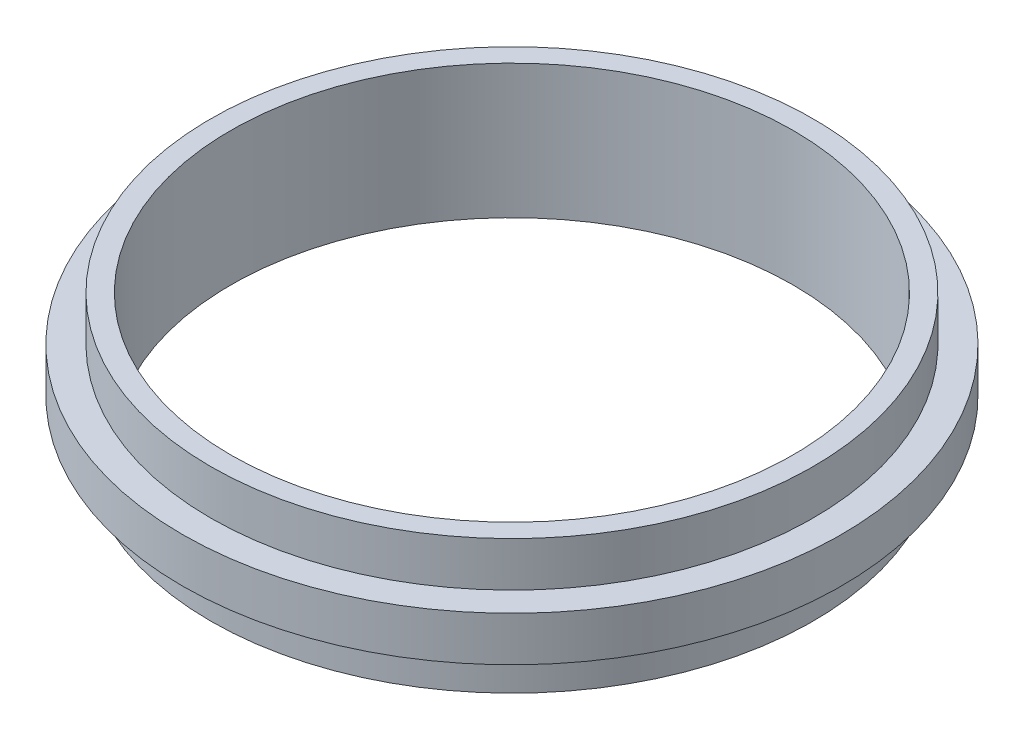
SolidWorks part; units mm, degrees
ref_plane "Front Plane" through (0, 0, 0) normal (0, 0, 1) x (1, 0, 0)
ref_plane "Top Plane" through (0, 0, 0) normal (0, 1, 0) x (1, 0, 0)
ref_plane "Right Plane" through (0, 0, 0) normal (1, 0, 0) x (0, 0, -1)
sketch "Sketch1" plane through (0, 0, 0) normal (0, 1, 0) x (1, 0, 0)
  circle A0 centre (0, 0) radius 93.7895
  circle A1 centre (0, 0) radius 80.01
  dimension "D1" = 187.579
  dimension "D2" = 160.02
extrude "Boss-Extrude1" add sketch "Sketch1" along normal mid plane 12.7
sketch "Sketch2" plane through (0, 6.35, 0) normal (0, 1, 0) x (1, 0, 0)
  circle A0 centre (0, 0) radius 88.9
  circle A1 centre (0, 0) radius 85.725
  dimension "D1" = 177.8
  dimension "D2" = 171.45
extrude "Cut-Extrude1" [suppressed] cut sketch "Sketch2" against normal blind 6.35
mirror "Mirror1" [suppressed] about plane through (0, 0, 0) normal (0, 1, 0)
sketch "Sketch3" plane through (0, 6.35, 0) normal (0, 1, 0) x (1, 0, 0)
  circle A0 centre (0, 0) radius 80.01
  circle A1 centre (0, 0) radius 85.725
  dimension "D1" = 171.45
  dimension "D2" = 160.02
extrude "Boss-Extrude2" add sketch "Sketch3" along normal blind 12.7
mirror "Mirror2" about plane through (0, 0, 0) normal (0, 1, 0) of "Boss-Extrude2"
